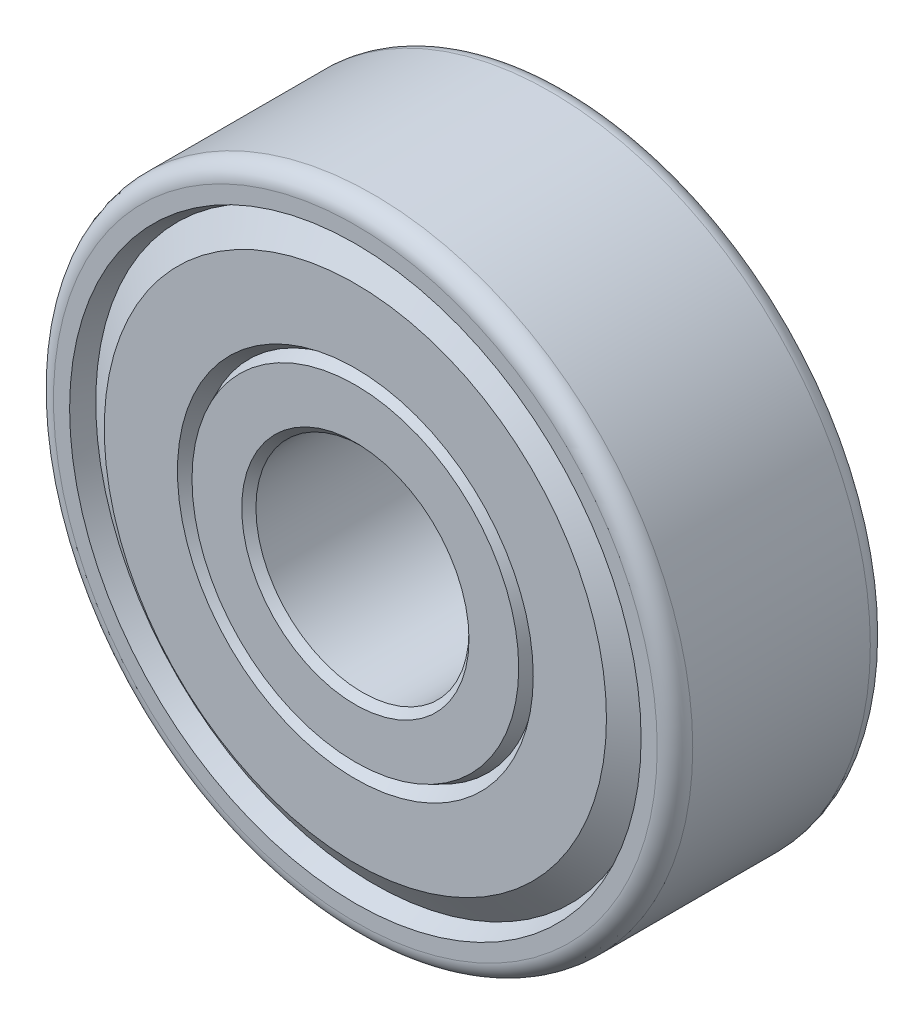
SolidWorks part; units mm, degrees
ref_plane "Plan de face" through (0, 0, 0) normal (0, 0, 1) x (1, 0, 0)
ref_plane "Plan de dessus" through (0, 0, 0) normal (0, 1, 0) x (1, 0, 0)
ref_plane "Plan de droite" through (0, 0, 0) normal (1, 0, 0) x (0, 0, -1)
sketch "Esquisse1" plane through (0, 0, 0) normal (0, 1, 0) x (1, 0, 0)
  line L0 (5.08, 4.7625) -> (4.7625, 4.445)
  line L1 (4.7625, 4.445) -> (4.7625, -4.445)
  line L2 (4.7625, -4.445) -> (5.08, -4.7625)
  line L3 (5.08, -4.7625) -> (7.3025, -4.7625)
  line L4 (7.3025, -4.7625) -> (7.5537, -4.1813)
  line L5 (7.5537, -4.1813) -> (7.9521, -4.7625)
  line L6 (7.9521, -4.7625) -> (11.2241, -4.7625)
  line L7 (11.2241, -4.7625) -> (12.4381, -3.9302)
  line L8 (12.4381, -3.9302) -> (12.7729, -4.7625)
  line L9 (12.7729, -4.7625) -> (13.4937, -4.7625)
  line L10 (14.2875, -3.9688) -> (14.2875, 3.9687)
  line L11 (13.4937, 4.7625) -> (12.7729, 4.7625)
  line L12 (12.7729, 4.7625) -> (12.4381, 3.9302)
  line L13 (12.4381, 3.9302) -> (11.2241, 4.7625)
  line L14 (11.2241, 4.7625) -> (7.9521, 4.7625)
  line L15 (7.9521, 4.7625) -> (7.5537, 4.1813)
  line L16 (7.5537, 4.1813) -> (7.3025, 4.7625)
  line L17 (7.3025, 4.7625) -> (5.08, 4.7625)
  line L18 (0, 4.7638) -> (0, -4.7638) construction
  arc A0 (13.4937, -4.7625) -> (14.2875, -3.9688) centre (13.4937, -3.9688) ccw
  arc A1 (14.2875, 3.9687) -> (13.4937, 4.7625) centre (13.4937, 3.9687) ccw
revolve "Révolution1" add sketch "Esquisse1" angle 360 about L18
